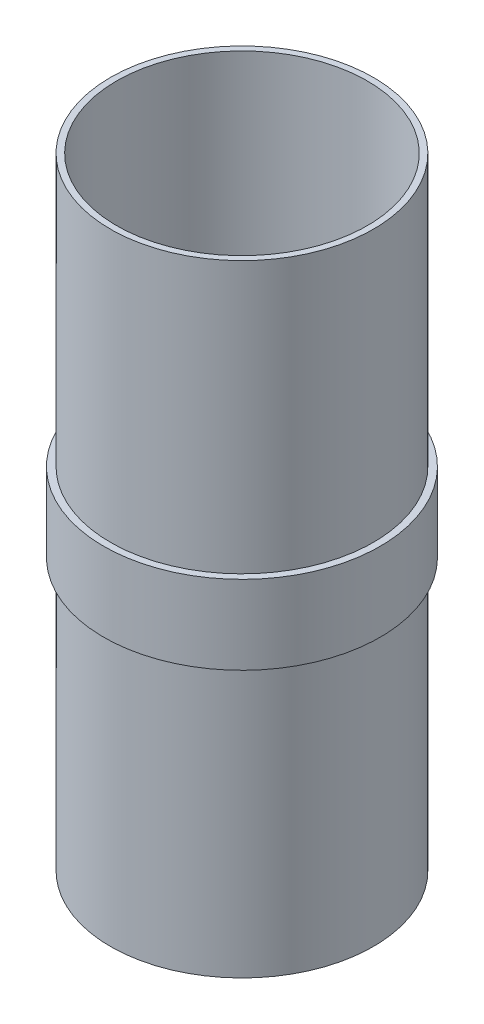
SolidWorks part; units mm, degrees
ref_plane "Front Plane" through (0, 0, 0) normal (0, 0, 1) x (1, 0, 0)
ref_plane "Top Plane" through (0, 0, 0) normal (0, 1, 0) x (1, 0, 0)
ref_plane "Right Plane" through (0, 0, 0) normal (1, 0, 0) x (0, 0, -1)
sketch "Sketch1" plane through (0, 0, 0) normal (0, 0, 1) x (1, 0, 0)
  line L0 (0, 0) -> (0, 233.3625)
  line L1 (0, 233.3625) -> (-2.286, 233.3625)
  line L2 (-2.286, 233.3625) -> (-2.286, 131.4768)
  line L3 (-2.286, 131.4768) -> (-4.826, 131.4768)
  line L4 (-4.826, 131.4768) -> (-4.826, 101.8858)
  line L5 (-4.826, 101.8858) -> (-2.286, 101.8858)
  line L6 (-2.286, 101.8858) -> (-2.286, 0)
  line L7 (-2.286, 0) -> (0, 0)
  line L8 (47.1043, 199.644) -> (47.1043, -28.956) construction
  dimension "D1" = 233.3625
  dimension "D2" = 29.591
  dimension "D3" = 2.286
  dimension "D4" = 2.54
  dimension "D5" = 49.3903
revolve "Revolve1" add sketch "Sketch1" angle 360 about L8
